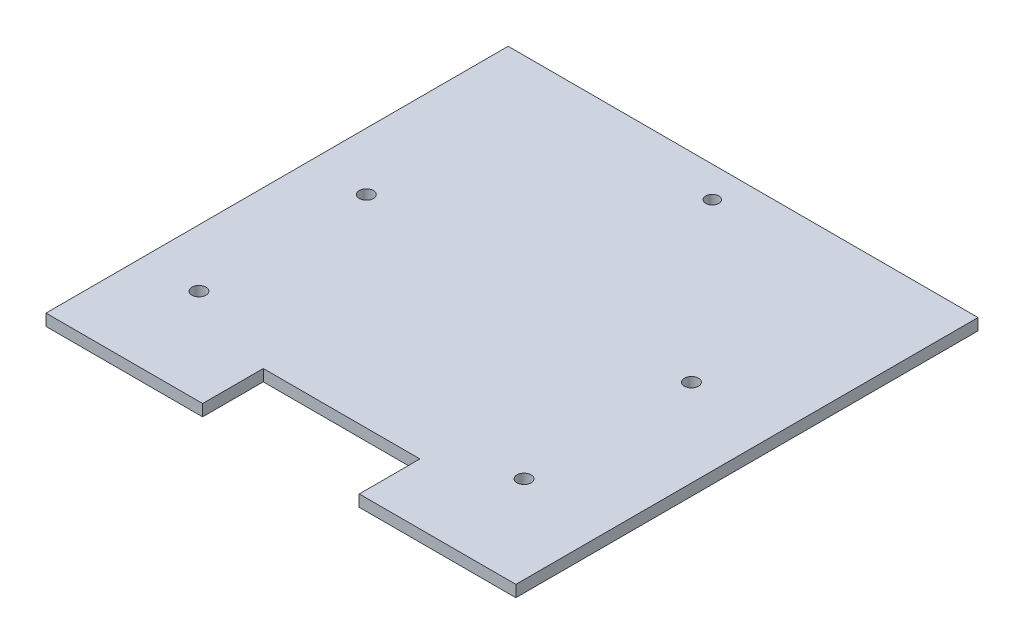
SolidWorks part; units mm, degrees
ref_plane "Front Plane" through (0, 0, 0) normal (0, 0, 1) x (1, 0, 0)
ref_plane "Top Plane" through (0, 0, 0) normal (0, 1, 0) x (1, 0, 0)
ref_plane "Right Plane" through (0, 0, 0) normal (1, 0, 0) x (0, 0, -1)
sketch "Sketch1" plane through (0, 0, 0) normal (0, 1, 0) x (1, 0, 0)
  line L1 (-96.84, -95.25) -> (96.84, -95.25)
  line L2 (-96.84, -95.25) -> (-96.84, 95.25)
  line L3 (-96.84, 95.25) -> (96.84, 95.25)
  line L4 (96.84, -95.25) -> (96.84, 95.25)
  line L5 (-96.84, -95.25) -> (96.84, 95.25) construction
  line L6 (-96.84, 95.25) -> (96.84, -95.25) construction
  point P0 (0, 0)
  dimension "D1" = 193.68
  dimension "D2" = 190.5
extrude "Boss-Extrude1" add sketch "Sketch1" along normal blind 4.78
sketch "Sketch2" plane through (0, 4.78, 0) normal (0, 1, 0) x (1, 0, 0)
  line L0 (96.84, 95.25) -> (-96.84, 95.25) construction
  line L1 (96.84, -95.25) -> (96.84, 95.25) construction
  circle A0 centre (0, 82.55) radius 2.6797
  point P4 (0, 95.25)
  dimension "D1" = 5.3594
  dimension "D2" = 12.7
  dimension "D3" = 96.84
extrude "Cut-Extrude1" cut sketch "Sketch2" against normal through all
sketch "Sketch3" plane through (0, 4.78, 0) normal (0, 1, 0) x (1, 0, 0)
  line L0 (0, -95.25) -> (-32.28, -95.25)
  line L1 (-96.84, -95.25) -> (96.84, -95.25) construction
  line L2 (-32.28, -95.25) -> (-32.28, -70.25)
  line L3 (-32.28, -70.25) -> (32.28, -70.25)
  line L4 (32.28, -70.25) -> (32.28, -95.25)
  line L5 (32.28, -95.25) -> (0, -95.25)
  line L6 (96.84, -95.25) -> (96.84, 95.25) construction
  dimension "D1" = 64.56
  dimension "D2" = 64.56
  dimension "D3" = 25
extrude "Cut-Extrude2" cut sketch "Sketch3" against normal through all
sketch "Sketch4" plane through (0, 4.78, 0) normal (0, 1, 0) x (1, 0, 0)
  line L0 (32.28, -70.25) -> (-32.28, -70.25) construction
  line L1 (-84.14, -63.9) -> (75.86, -63.9)
  line L2 (-84.14, -63.9) -> (-84.14, 26.1)
  line L3 (-84.14, 26.1) -> (75.86, 26.1)
  line L4 (75.86, -63.9) -> (75.86, 26.1)
  line L5 (-96.84, 95.25) -> (-96.84, -95.25) construction
  circle A1 centre (-73.14, -55.9) radius 2.8937
  circle A2 centre (-73.14, 13.1) radius 2.8937
  circle A4 centre (60.86, 13.1) radius 2.8937
  circle A5 centre (60.86, -55.9) radius 2.8937
  dimension "D5" = 5.7874
  dimension "D8" = 11
  dimension "D9" = 8
  dimension "D12" = 77
  dimension "D13" = 11
  dimension "D14" = 145
  dimension "D15" = 8
  dimension "D16" = 145
  dimension "D17" = 77
  dimension "D1" = 6.35
  dimension "D2" = 90
  dimension "D3" = 160
  dimension "D4" = 12.7
extrude "Cut-Extrude3" cut sketch "Sketch4" against normal through all contours A2 | A1 | A5 | A4
